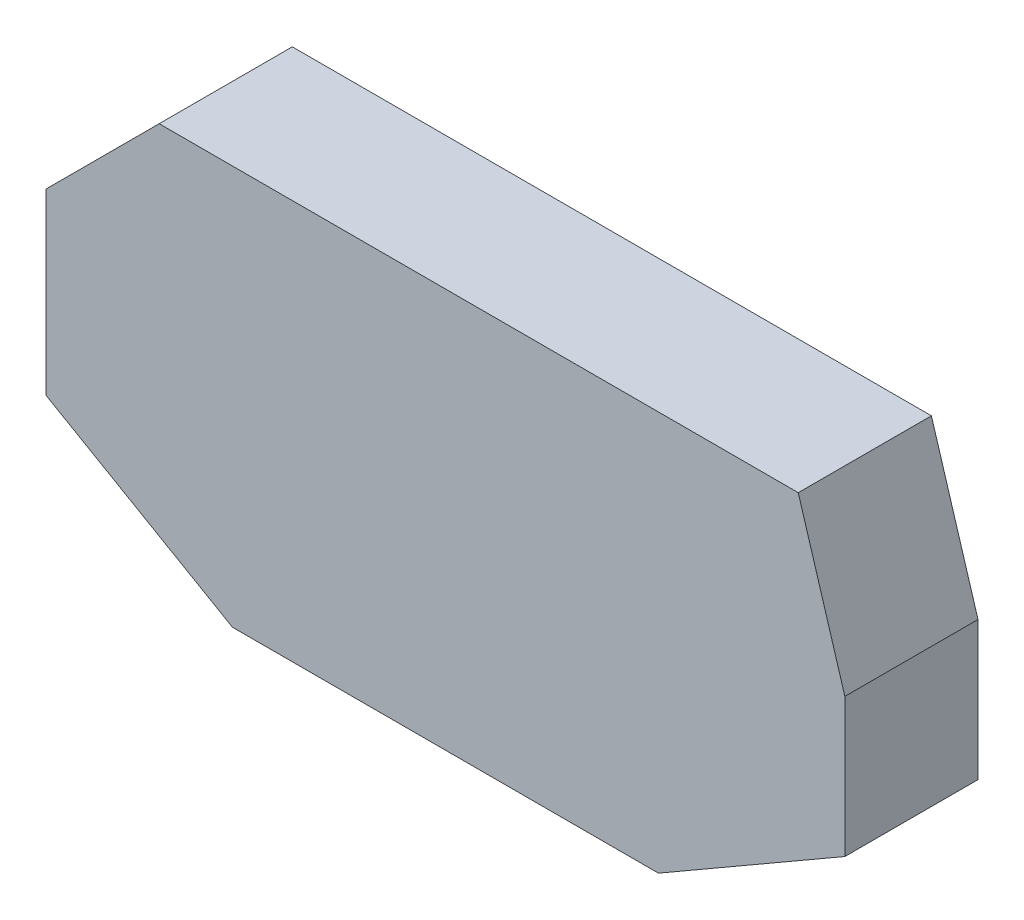
SolidWorks part; units mm, degrees
ref_plane "Plan de face" through (0, 0, 0) normal (0, 0, 1) x (1, 0, 0)
ref_plane "Plan de dessus" through (0, 0, 0) normal (0, 1, 0) x (1, 0, 0)
ref_plane "Plan de droite" through (0, 0, 0) normal (1, 0, 0) x (0, 0, -1)
sketch "Esquisse5" plane through (0, 0, 0) normal (0, 0, 1) x (1, 0, 0)
  line L0 (-60, 13) -> (-43, 30)
  line L1 (-32, -30) -> (32, -30)
  line L2 (-60, -13.8342) -> (-60, 13)
  line L3 (-43, 30) -> (53, 30)
  line L4 (60, -13.8342) -> (60, 7)
  line L5 (-60, -30) -> (60, 30) construction
  line L6 (-60, 30) -> (60, -30) construction
  line L7 (60, 7) -> (53, 30)
  line L8 (-60, -13.8342) -> (-32, -30)
  line L9 (32, -30) -> (60, -13.8342)
  point P0 (0, 0)
  dimension "D1" = 120
  dimension "D2" = 60
  dimension "D3" = 23
  dimension "D4" = 7
  dimension "D6" = 28
  dimension "D7" = 30
  dimension "D8" = 28
  dimension "D9" = 30
extrude "Boss.-Extru.6" add sketch "Esquisse5" along normal blind 20
